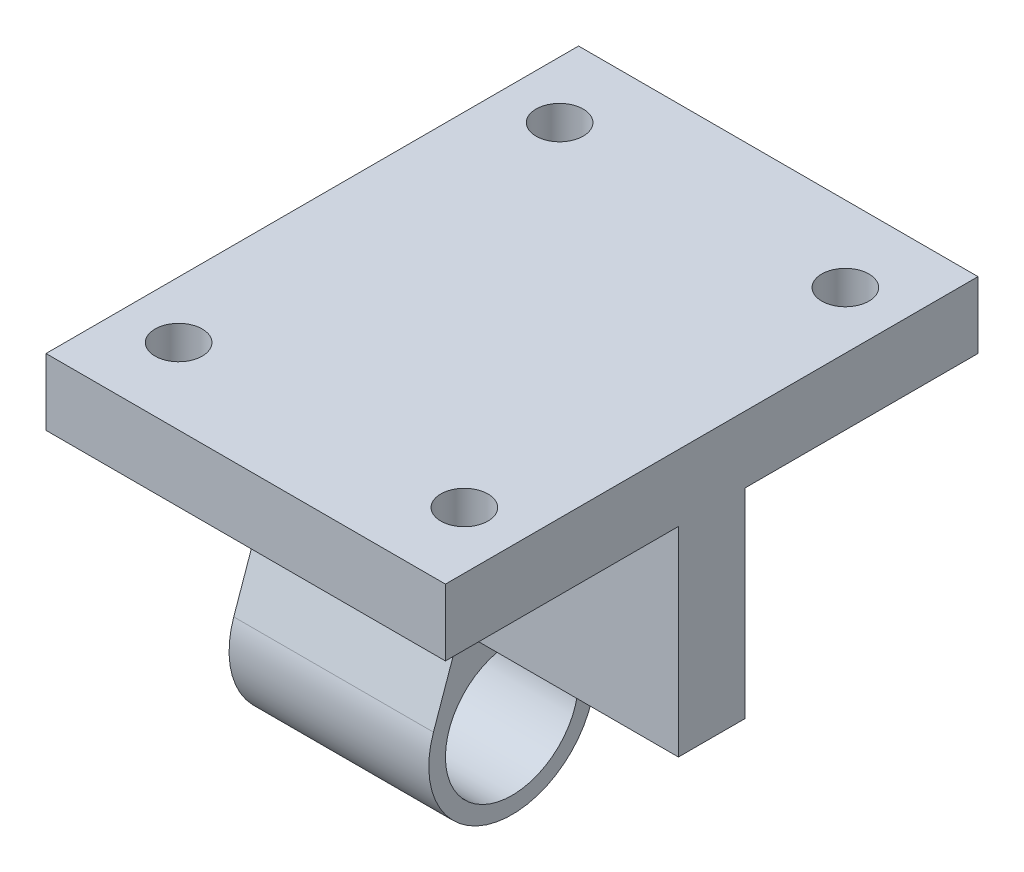
SolidWorks part; units mm, degrees
ref_plane "Front Plane" through (0, 0, 0) normal (0, 0, 1) x (1, 0, 0)
ref_plane "Top Plane" through (0, 0, 0) normal (0, 1, 0) x (1, 0, 0)
ref_plane "Right Plane" through (0, 0, 0) normal (1, 0, 0) x (0, 0, -1)
sketch "Sketch1" plane through (0, 0, 0) normal (1, 0, 0) x (0, 0, -1)
  line L0 (0, 25.4) -> (0, 0) construction
  line L3 (-3.175, 0) -> (3.175, 0)
  line L4 (3.175, 19.05) -> (3.175, 0)
  line L5 (-3.175, 19.05) -> (-25.4, 19.05)
  line L6 (-25.4, 25.4) -> (-25.4, 19.05)
  line L7 (-25.4, 25.4) -> (25.4, 25.4)
  line L10 (25.4, 25.4) -> (25.4, 19.05)
  line L11 (-3.175, 19.05) -> (-3.175, 0)
  line L13 (3.175, 19.05) -> (25.4, 19.05)
  point P0 (0, 0)
  point P6 (0, 9.7518)
  point P13 (1.0089, -12.079)
  point P14 (0, 0)
  dimension "D1" = 3.175
  dimension "D2" = 19.05
  dimension "D3" = 6.35
  dimension "D4" = 25.4
  dimension "D5" = 90
extrude "Boss-Extrude1" add sketch "Sketch1" along normal blind 38.1
sketch "Sketch2" plane through (0, 0, 0) normal (-1, 0, 0) x (0, 0, 1)
  line L0 (0, 0) -> (0, -7.9375) construction
  line L1 (7.4908, -5.3123) -> (3.5323, 5.9831)
  line L2 (3.175, 19.05) -> (3.175, 0) construction
  line L3 (-7.4908, -5.3123) -> (-3.5323, 5.9831)
  line L4 (-3.175, 0) -> (-3.175, 19.05) construction
  line L5 (-3.175, 7.0028) -> (-3.175, 0)
  line L6 (-3.175, 0) -> (3.175, 0)
  line L7 (3.175, 0) -> (3.175, 7.0028)
  line L8 (3.175, 8.0832) -> (3.175, 19.05)
  line L9 (-3.175, 8.0832) -> (-3.175, 19.05)
  circle A0 centre (0, -7.9375) radius 6.35
  arc A1 (-7.4908, -5.3123) -> (7.4908, -5.3123) centre (0, -7.9375) ccw
  arc A2 (3.175, 8.0832) -> (3.5323, 5.9831) centre (9.525, 8.0832) ccw
  arc A3 (-3.175, 8.0832) -> (-3.5323, 5.9831) centre (-9.525, 8.0832) cw
  dimension "D2" = 12.7
  dimension "D3" = 6.35
  dimension "D4" = 6.35
  dimension "D6" = 7.9375
  dimension "D5" = 11.969
extrude "Boss-Extrude2" add sketch "Sketch2" against normal blind 19.05
sketch "Sketch3" plane through (0, 25.4, 0) normal (0, 1, 0) x (1, 0, 0)
  line L0 (38.1, -25.4) -> (0, 25.4) construction
  line L1 (0, -25.4) -> (38.1, 25.4) construction
  line L2 (34.925, -18.1695) -> (38.1, -18.1695) construction
  line L3 (38.1, 25.4) -> (38.1, -25.4) construction
  line L4 (3.175, -18.1695) -> (0, -18.1695) construction
  line L5 (0, 25.4) -> (0, -25.4) construction
  line L6 (3.175, 18.1695) -> (0, 18.1695) construction
  line L7 (34.925, 18.1695) -> (38.1, 18.1695) construction
  circle A0 centre (5.4229, 18.1695) radius 2.2479
  circle A1 centre (32.6771, 18.1695) radius 2.2479
  circle A2 centre (32.6771, -18.1695) radius 2.2479
  circle A3 centre (5.4229, -18.1695) radius 2.2479
  dimension "D1" = 4.4958
  dimension "D2" = 3.175
extrude "Cut-Extrude1" cut sketch "Sketch3" against normal through all
